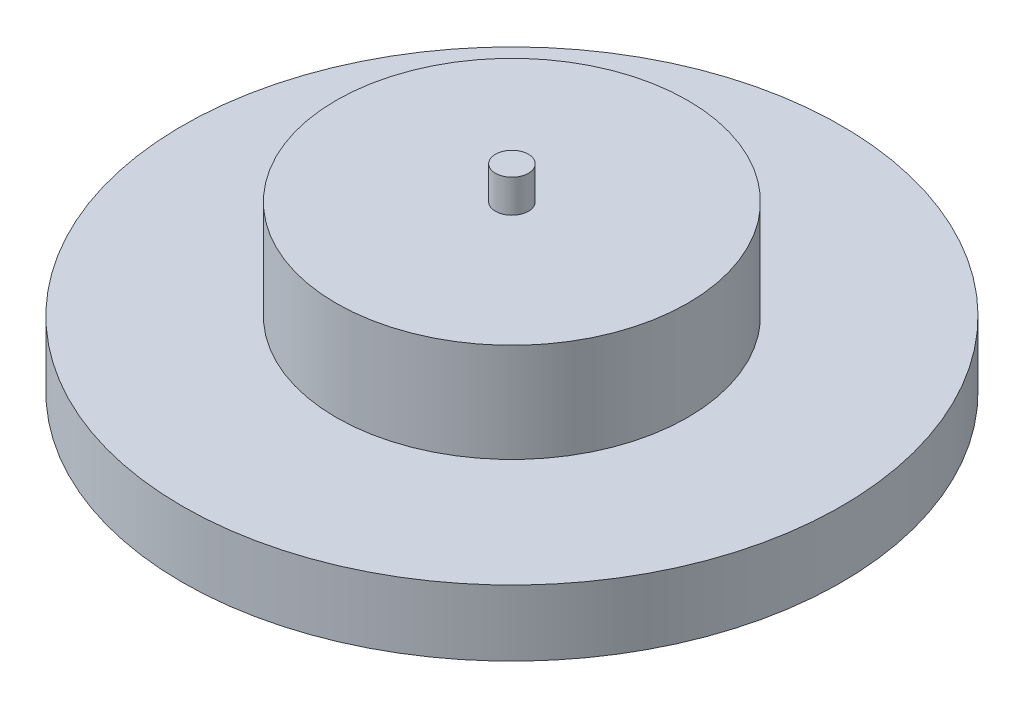
SolidWorks part; units mm, degrees
ref_plane "前视基准面" through (0, 0, 0) normal (0, 0, 1) x (1, 0, 0)
ref_plane "上视基准面" through (0, 0, 0) normal (0, 1, 0) x (1, 0, 0)
ref_plane "右视基准面" through (0, 0, 0) normal (1, 0, 0) x (0, 0, -1)
other "Configuration Table"
sketch "草图1" plane through (0, 0, 0) normal (0, 1, 0) x (1, 0, 0)
  circle A0 centre (0, 0) radius 15
  dimension "D1" = 30
extrude "凸台-拉伸1" add sketch "草图1" along normal blind 3
sketch "草图2" plane through (0, 3, 0) normal (0, 1, 0) x (1, 0, 0)
  circle A0 centre (0, 0) radius 8
  dimension "D1" = 16
extrude "凸台-拉伸2" add sketch "草图2" along normal blind 4.5
sketch "草图3" plane through (0, 7.5, 0) normal (0, 1, 0) x (1, 0, 0)
  circle A0 centre (0, 0) radius 0.75
  dimension "D1" = 1.5
extrude "凸台-拉伸3" add sketch "草图3" along normal blind 1.5
